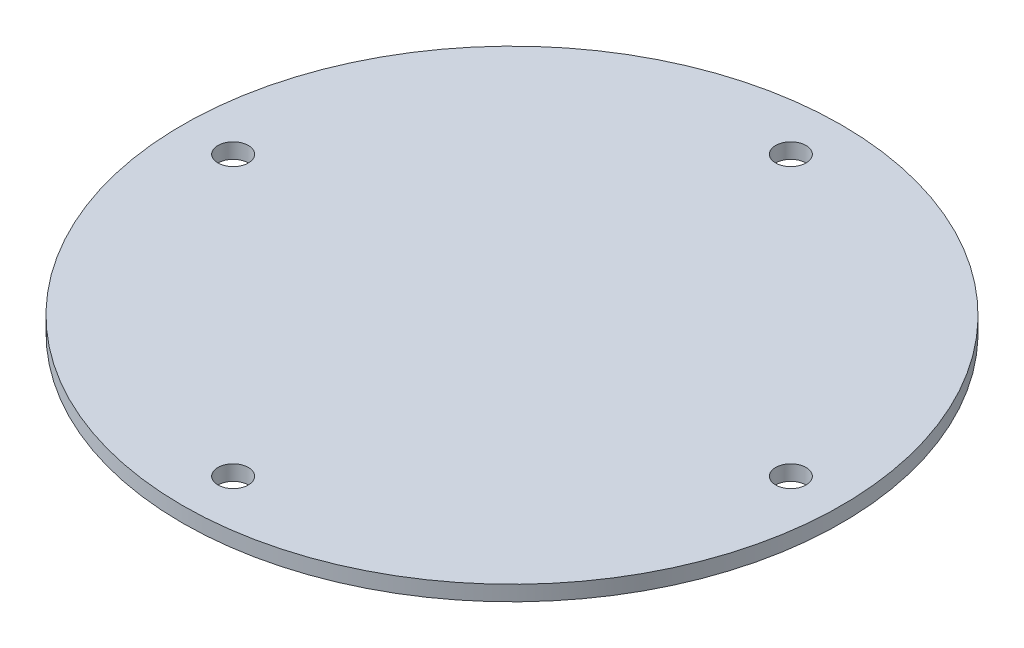
SolidWorks part; units mm, degrees
ref_plane "Front Plane" through (0, 0, 0) normal (0, 0, 1) x (1, 0, 0)
ref_plane "Top Plane" through (0, 0, 0) normal (0, 1, 0) x (1, 0, 0)
ref_plane "Right Plane" through (0, 0, 0) normal (1, 0, 0) x (0, 0, -1)
sketch "Sketch1" plane through (0, 0, 0) normal (0, 1, 0) x (1, 0, 0)
  circle A0 centre (0, 0) radius 65
  dimension "D1" = 130
extrude "Boss-Extrude1" add sketch "Sketch1" along normal blind 3
sketch "Sketch2" plane through (0, 3, 0) normal (0, 1, 0) x (1, 0, 0)
  circle A0 centre (0, 0) radius 55 construction
  circle A1 centre (0, 55) radius 3
  dimension "D1" = 110
  dimension "D2" = 6
extrude "Cut-Extrude1" cut sketch "Sketch2" against normal through all
pattern_circular "CirPattern1" count 4 over 360 about axis through (0, 0, 0) along (0, 1, 0) of "Cut-Extrude1"
